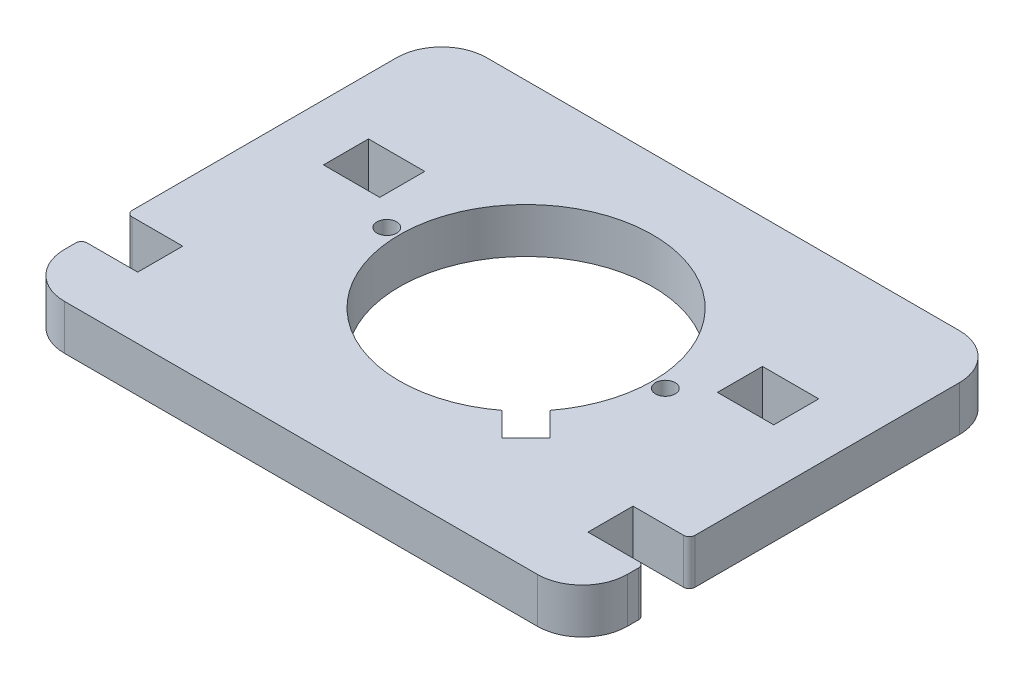
SolidWorks part; units mm, degrees
ref_plane "Front Plane" through (0, 0, 0) normal (0, 0, 1) x (1, 0, 0)
ref_plane "Top Plane" through (0, 0, 0) normal (0, 1, 0) x (1, 0, 0)
ref_plane "Right Plane" through (0, 0, 0) normal (1, 0, 0) x (0, 0, -1)
sketch "Sketch1" plane through (0, 0, 0) normal (0, 1, 0) x (1, 0, 0)
  line L0 (-8, 0) -> (-92, 0)
  line L1 (-100, 8) -> (-100, 10)
  line L2 (-100, 53) -> (-100, 67)
  line L3 (-92, 75) -> (-8, 75)
  line L4 (0, 67) -> (0, 53)
  line L5 (0, 0) -> (0, 11) construction
  line L6 (-74.74, 40) -> (-25.26, 40) construction
  line L7 (0, 43) -> (0, 20)
  line L8 (0, 52) -> (0, 539.5591) construction
  line L9 (0, 19) -> (0, 44) construction
  line L10 (0, 10) -> (0, 8)
  line L11 (-50, 40) -> (-23.2152, 13.2152) construction
  line L12 (-36.3535, 22.1108) -> (-32.1108, 17.8682)
  line L13 (-32.1108, 17.8682) -> (-29.9895, 19.9895)
  line L14 (-29.9895, 19.9895) -> (-27.8682, 22.1108)
  line L15 (-27.8682, 22.1108) -> (-32.1108, 26.3535)
  line L16 (-10, 52) -> (-20, 52)
  line L17 (-20, 52) -> (-20, 44)
  line L18 (-20, 44) -> (-10, 44)
  line L19 (0, 53) -> (0, 43)
  line L20 (-90, 52) -> (-80, 52)
  line L21 (-80, 52) -> (-80, 44)
  line L22 (-80, 44) -> (-90, 44)
  line L23 (-100, 53) -> (-100, 43)
  line L34 (-99, 52) -> (-90, 52)
  line L35 (-10, 52) -> (-1, 52)
  line L36 (-10, 52) -> (-10, 44)
  line L37 (-10, 44) -> (-1, 44)
  line L41 (-10, 19) -> (-1, 19)
  line L42 (-10, 19) -> (-10, 11)
  line L43 (-10, 11) -> (-1, 11)
  line L47 (-90, 52) -> (-90, 44)
  line L48 (-90, 44) -> (-99, 44)
  line L49 (-99, 19) -> (-90, 19)
  line L50 (-90, 19) -> (-90, 11)
  line L51 (-90, 11) -> (-99, 11)
  line L56 (-100, 20) -> (-100, 43)
  arc A0 (0, 67) -> (-8, 75) centre (-8, 67) ccw
  arc A1 (-92, 75) -> (-100, 67) centre (-92, 67) ccw
  arc A2 (0, 8) -> (-8, 0) centre (-8, 8) cw
  arc A3 (-100, 10) -> (-99, 11) centre (-99, 10) cw
  circle A4 centre (-50, 40) radius 24.74 construction
  circle A5 centre (-25.26, 40) radius 1.75
  circle A6 centre (-74.74, 40) radius 1.75
  arc A7 (-36.3535, 22.1108) -> (-32.1108, 26.3535) centre (-50, 40) cw
  arc A8 (-100, 20) -> (-99, 19) centre (-99, 20) ccw
  arc A9 (-100, 53) -> (-99, 52) centre (-99, 53) ccw
  arc A10 (-100, 43) -> (-99, 44) centre (-99, 43) cw
  arc A11 (0, 10) -> (-1, 11) centre (-1, 10) ccw
  arc A12 (-1, 19) -> (0, 20) centre (-1, 20) ccw
  arc A13 (0, 43) -> (-1, 44) centre (-1, 43) ccw
  arc A14 (0, 53) -> (-1, 52) centre (-1, 53) cw
  arc A22 (-92, 0) -> (-100, 8) centre (-92, 8) cw
  point P14 (0, 75)
  point P32 (-100, 19)
  point P34 (0, 0)
  point P37 (-100, 52)
  point P41 (-100, 44)
  point P118 (-100, 0)
  dimension "D15" = 6
  dimension "D16" = 3
  dimension "D17" = 1
  dimension "D31" = 8
  dimension "D8" = 45
  dimension "D9" = 49.48
  dimension "D10" = 3.5
  dimension "D13" = 8
  dimension "D4" = 75
  dimension "D5" = 100
  dimension "D6" = 40
  dimension "D7" = 50
  dimension "D11" = 10
  dimension "D12" = 8
  dimension "D14" = 45
  dimension "D18" = 10
  dimension "D19" = 10
  dimension "D20" = 25
  dimension "D21" = 11
  dimension "D23" = 10
extrude "Boss-Extrude2" add sketch "Sketch1" along normal blind 8 contours A22 L0 A2 L10 A11 L43 L42 L41 A12 L7 A13 L37 L36 L35 A14 L4 A0 L3 A1 L2 A9 L34 L47 L48 A10 L56 A8 L49 L50 L51 A3 L1 A6 A7 A5 L15 L14 L13 L12 | L23 A10 L48 L47 L34 A9 | L19 A14 L35 L36 L37 A13
